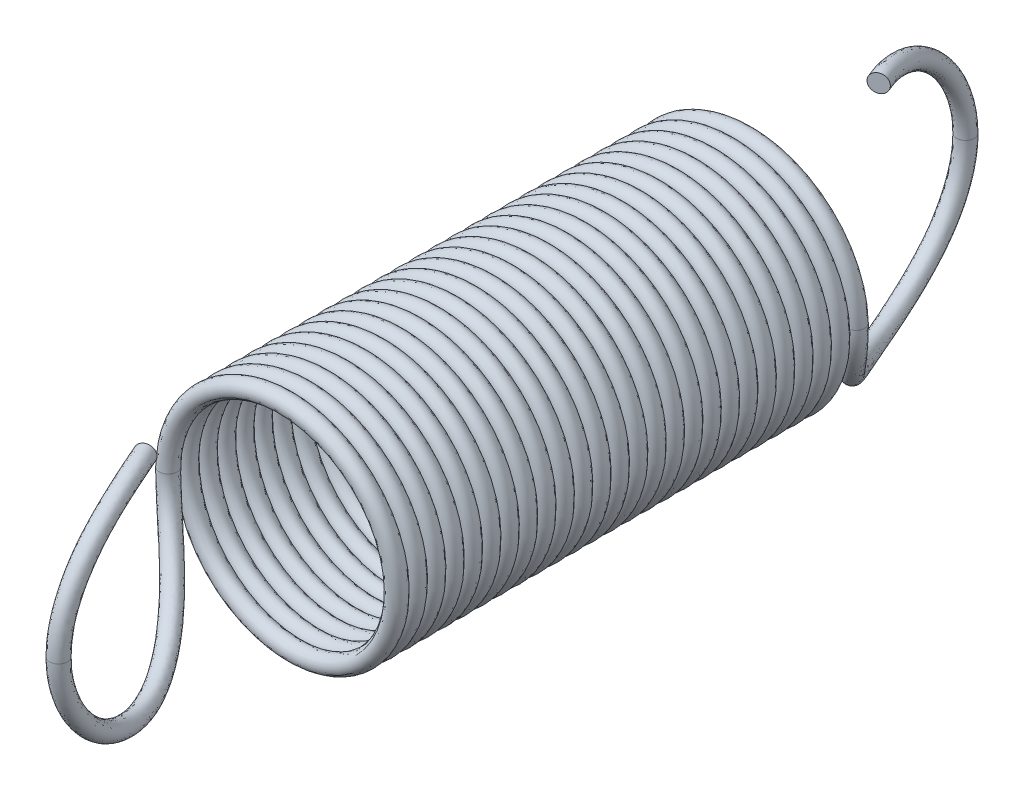
SolidWorks part; units mm, degrees
ref_plane "Front Plane" through (0, 0, 0) normal (0, 0, 1) x (1, 0, 0)
ref_plane "Top Plane" through (0, 0, 0) normal (0, 1, 0) x (1, 0, 0)
ref_plane "Right Plane" through (0, 0, 0) normal (1, 0, 0) x (0, 0, -1)
sketch "Sketch1" plane through (0, 0, 0) normal (1, 0, 0) x (0, 0, -1)
  line L0 (-7.5, 0) -> (7.5, 0) construction
  line L1 (7.5, 0) -> (40.99, 0) construction
  line L2 (-7.5, 2) -> (-7.5, -2) construction
  point P4 (0, 0)
  point P6 (-7.2, 0)
  point P9 (-7.5, 0)
  dimension "OD" = 4
  dimension "Wire Diameter" = 0.3
  dimension "Length" = 15
  dimension "Extended Length" = 48.49
sketch "Sketch2" plane through (0, 0, 0) normal (1, 0, 0) x (0, 0, -1)
  line L1 (-7.5, 0) -> (-7.8, 0) construction
  line L2 (-5.8, -1.7) -> (-5.8, -2) construction
  line L3 (0, 0) -> (0, 2) construction
  line L4 (-7.5, 0) -> (-7.2, 0) construction
  line L5 (-7.5, 0) -> (7.5, 0) construction
  line L6 (5.8, -1.7) -> (5.8, -2) construction
  line L7 (7.5, 0) -> (7.8, 0) construction
  line L8 (-5.8, -1.7) -> (5.8, -1.7) construction
  line L9 (-5.8, -2) -> (5.8, -2) construction
  line L10 (-3.8, 0) -> (-4.1, 0) construction
  line L11 (4.1, 0) -> (3.8, 0) construction
  line L12 (-7.5, 2) -> (-5.8, 2) construction
  circle A0 centre (-5.8, 0) radius 1.7 construction
  circle A2 centre (-5.8, 0) radius 2 construction
  circle A3 centre (5.8, 0) radius 2 construction
  circle A4 centre (5.8, 0) radius 1.7 construction
  point P7 (-2.6, 0)
  point P8 (-5.8, -1.85)
  point P10 (-7.65, 0)
  point P28 (7.65, 0)
  point P33 (-3.95, 0)
  point P34 (3.95, 0)
  point P35 (2.6, 0)
  dimension "OD" = 4
  dimension "D1" = 7.9
  dimension "D2" = 1.2
  dimension "D3" = 1.2
ref_plane "Plane1" through (0, 0, 3.95) normal (0, 0, 1) x (1, 0, 0)
sketch "Sketch3" plane through (0, 0, 3.95) normal (0, 0, 1) x (1, 0, 0)
  circle A0 centre (0, 0) radius 1.85
curve "Helix/Spiral1" pitch 0.3098 height 7.9 turns 25.5 parameters "Height"=7.9, "Pitch"=0.3098
sketch "Sketch4" plane through (0, 0, 0) normal (0, 1, 0) x (1, 0, 0)
  circle A0 centre (-1.85, -3.95) radius 0.15
  spline S0 degree 3 poles (-1.85, -3.95) (-1.85, -3.9436) (-1.7537, -3.9306) (-1.3422, -3.9113) (-0.7264, -3.8919) (0, -3.8725) (0.7264, -3.8532) (1.3422, -3.8338) (1.7537, -3.8145) (1.8982, -3.7951) (1.7537, -3.7757) (1.3422, -3.7564) (0.7264, -3.737) (0, -3.7176) (-0.7264, -3.6983) (-1.3422, -3.6789) (-1.7537, -3.6596) (-1.8982, -3.6402) (-1.7537, -3.6208) (-1.3422, -3.6015) (-0.7264, -3.5821) (0, -3.5627) (0.7264, -3.5434) (1.3422, -3.524) (1.7537, -3.5047) (1.8982, -3.4853) (1.7537, -3.4659) (1.3422, -3.4466) (0.7264, -3.4272) (0, -3.4078) (-0.7264, -3.3885) (-1.3422, -3.3691) (-1.7537, -3.3498) (-1.8982, -3.3304) (-1.7537, -3.311) (-1.3422, -3.2917) (-0.7264, -3.2723) (0, -3.2529) (0.7264, -3.2336) (1.3422, -3.2142) (1.7537, -3.1949) (1.8982, -3.1755) (1.7537, -3.1561) (1.3422, -3.1368) (0.7264, -3.1174) (0, -3.098) (-0.7264, -3.0787) (-1.3422, -3.0593) (-1.7537, -3.04) (-1.8982, -3.0206) (-1.7537, -3.0012) (-1.3422, -2.9819) (-0.7264, -2.9625) (0, -2.9431) (0.7264, -2.9238) (1.3422, -2.9044) (1.7537, -2.885) (1.8982, -2.8657) (1.7537, -2.8463) (1.3422, -2.827) (0.7264, -2.8076) (0, -2.7882) (-0.7264, -2.7689) (-1.3422, -2.7495) (-1.7537, -2.7301) (-1.8982, -2.7108) (-1.7537, -2.6914) (-1.3422, -2.6721) (-0.7264, -2.6527) (0, -2.6333) (0.7264, -2.614) (1.3422, -2.5946) (1.7537, -2.5752) (1.8982, -2.5559) (1.7537, -2.5365) (1.3422, -2.5172) (0.7264, -2.4978) (0, -2.4784) (-0.7264, -2.4591) (-1.3422, -2.4397) (-1.7537, -2.4203) (-1.8982, -2.401) (-1.7537, -2.3816) (-1.3422, -2.3623) (-0.7264, -2.3429) (0, -2.3235) (0.7264, -2.3042) (1.3422, -2.2848) (1.7537, -2.2654) (1.8982, -2.2461) (1.7537, -2.2267) (1.3422, -2.2074) (0.7264, -2.188) (0, -2.1686) (-0.7264, -2.1493) (-1.3422, -2.1299) (-1.7537, -2.1105) (-1.8982, -2.0912) (-1.7537, -2.0718) (-1.3422, -2.0525) (-0.7264, -2.0331) (0, -2.0137) (0.7264, -1.9944) (1.3422, -1.975) (1.7537, -1.9556) (1.8982, -1.9363) (1.7537, -1.9169) (1.3422, -1.8975) (0.7264, -1.8782) (0, -1.8588) (-0.7264, -1.8395) (-1.3422, -1.8201) (-1.7537, -1.8007) (-1.8982, -1.7814) (-1.7537, -1.762) (-1.3422, -1.7426) (-0.7264, -1.7233) (0, -1.7039) (0.7264, -1.6846) (1.3422, -1.6652) (1.7537, -1.6458) (1.8982, -1.6265) (1.7537, -1.6071) (1.3422, -1.5877) (0.7264, -1.5684) (0, -1.549) (-0.7264, -1.5297) (-1.3422, -1.5103) (-1.7537, -1.4909) (-1.8982, -1.4716) (-1.7537, -1.4522) (-1.3422, -1.4328) (-0.7264, -1.4135) (0, -1.3941) (0.7264, -1.3748) (1.3422, -1.3554) (1.7537, -1.336) (1.8982, -1.3167) (1.7537, -1.2973) (1.3422, -1.2779) (0.7264, -1.2586) (0, -1.2392) (-0.7264, -1.2199) (-1.3422, -1.2005) (-1.7537, -1.1811) (-1.8982, -1.1618) (-1.7537, -1.1424) (-1.3422, -1.123) (-0.7264, -1.1037) (0, -1.0843) (0.7264, -1.065) (1.3422, -1.0456) (1.7537, -1.0262) (1.8982, -1.0069) (1.7537, -0.9875) (1.3422, -0.9681) (0.7264, -0.9488) (0, -0.9294) (-0.7264, -0.91) (-1.3422, -0.8907) (-1.7537, -0.8713) (-1.8982, -0.852) (-1.7537, -0.8326) (-1.3422, -0.8132) (-0.7264, -0.7939) (0, -0.7745) (0.7264, -0.7551) (1.3422, -0.7358) (1.7537, -0.7164) (1.8982, -0.6971) (1.7537, -0.6777) (1.3422, -0.6583) (0.7264, -0.639) (0, -0.6196) (-0.7264, -0.6002) (-1.3422, -0.5809) (-1.7537, -0.5615) (-1.8982, -0.5422) (-1.7537, -0.5228) (-1.3422, -0.5034) (-0.7264, -0.4841) (0, -0.4647) (0.7264, -0.4453) (1.3422, -0.426) (1.7537, -0.4066) (1.8982, -0.3873) (1.7537, -0.3679) (1.3422, -0.3485) (0.7264, -0.3292) (0, -0.3098) (-0.7264, -0.2904) (-1.3422, -0.2711) (-1.7537, -0.2517) (-1.8982, -0.2324) (-1.7537, -0.213) (-1.3422, -0.1936) (-0.7264, -0.1743) (0, -0.1549) (0.7264, -0.1355) (1.3422, -0.1162) (1.7537, -0.0968) (1.8982, -0.0775) (1.7537, -0.0581) (1.3422, -0.0387) (0.7264, -0.0194) (0, 0) (-0.7264, 0.0194) (-1.3422, 0.0387) (-1.7537, 0.0581) (-1.8982, 0.0775) (-1.7537, 0.0968) (-1.3422, 0.1162) (-0.7264, 0.1355) (0, 0.1549) (0.7264, 0.1743) (1.3422, 0.1936) (1.7537, 0.213) (1.8982, 0.2324) (1.7537, 0.2517) (1.3422, 0.2711) (0.7264, 0.2904) (0, 0.3098) (-0.7264, 0.3292) (-1.3422, 0.3485) (-1.7537, 0.3679) (-1.8982, 0.3873) (-1.7537, 0.4066) (-1.3422, 0.426) (-0.7264, 0.4453) (0, 0.4647) (0.7264, 0.4841) (1.3422, 0.5034) (1.7537, 0.5228) (1.8982, 0.5422) (1.7537, 0.5615) (1.3422, 0.5809) (0.7264, 0.6002) (0, 0.6196) (-0.7264, 0.639) (-1.3422, 0.6583) (-1.7537, 0.6777) (-1.8982, 0.6971) (-1.7537, 0.7164) (-1.3422, 0.7358) (-0.7264, 0.7551) (0, 0.7745) (0.7264, 0.7939) (1.3422, 0.8132) (1.7537, 0.8326) (1.8982, 0.852) (1.7537, 0.8713) (1.3422, 0.8907) (0.7264, 0.91) (0, 0.9294) (-0.7264, 0.9488) (-1.3422, 0.9681) (-1.7537, 0.9875) (-1.8982, 1.0069) (-1.7537, 1.0262) (-1.3422, 1.0456) (-0.7264, 1.065) (0, 1.0843) (0.7264, 1.1037) (1.3422, 1.123) (1.7537, 1.1424) (1.8982, 1.1618) (1.7537, 1.1811) (1.3422, 1.2005) (0.7264, 1.2199) (0, 1.2392) (-0.7264, 1.2586) (-1.3422, 1.2779) (-1.7537, 1.2973) (-1.8982, 1.3167) (-1.7537, 1.336) (-1.3422, 1.3554) (-0.7264, 1.3748) (0, 1.3941) (0.7264, 1.4135) (1.3422, 1.4328) (1.7537, 1.4522) (1.8982, 1.4716) (1.7537, 1.4909) (1.3422, 1.5103) (0.7264, 1.5297) (0, 1.549) (-0.7264, 1.5684) (-1.3422, 1.5877) (-1.7537, 1.6071) (-1.8982, 1.6265) (-1.7537, 1.6458) (-1.3422, 1.6652) (-0.7264, 1.6846) (0, 1.7039) (0.7264, 1.7233) (1.3422, 1.7426) (1.7537, 1.762) (1.8982, 1.7814) (1.7537, 1.8007) (1.3422, 1.8201) (0.7264, 1.8395) (0, 1.8588) (-0.7264, 1.8782) (-1.3422, 1.8975) (-1.7537, 1.9169) (-1.8982, 1.9363) (-1.7537, 1.9556) (-1.3422, 1.975) (-0.7264, 1.9944) (0, 2.0137) (0.7264, 2.0331) (1.3422, 2.0525) (1.7537, 2.0718) (1.8982, 2.0912) (1.7537, 2.1105) (1.3422, 2.1299) (0.7264, 2.1493) (0, 2.1686) (-0.7264, 2.188) (-1.3422, 2.2074) (-1.7537, 2.2267) (-1.8982, 2.2461) (-1.7537, 2.2654) (-1.3422, 2.2848) (-0.7264, 2.3042) (0, 2.3235) (0.7264, 2.3429) (1.3422, 2.3623) (1.7537, 2.3816) (1.8982, 2.401) (1.7537, 2.4203) (1.3422, 2.4397) (0.7264, 2.4591) (0, 2.4784) (-0.7264, 2.4978) (-1.3422, 2.5172) (-1.7537, 2.5365) (-1.8982, 2.5559) (-1.7537, 2.5752) (-1.3422, 2.5946) (-0.7264, 2.614) (0, 2.6333) (0.7264, 2.6527) (1.3422, 2.6721) (1.7537, 2.6914) (1.8982, 2.7108) (1.7537, 2.7301) (1.3422, 2.7495) (0.7264, 2.7689) (0, 2.7882) (-0.7264, 2.8076) (-1.3422, 2.827) (-1.7537, 2.8463) (-1.8982, 2.8657) (-1.7537, 2.885) (-1.3422, 2.9044) (-0.7264, 2.9238) (0, 2.9431) (0.7264, 2.9625) (1.3422, 2.9819) (1.7537, 3.0012) (1.8982, 3.0206) (1.7537, 3.04) (1.3422, 3.0593) (0.7264, 3.0787) (0, 3.098) (-0.7264, 3.1174) (-1.3422, 3.1368) (-1.7537, 3.1561) (-1.8982, 3.1755) (-1.7537, 3.1949) (-1.3422, 3.2142) (-0.7264, 3.2336) (0, 3.2529) (0.7264, 3.2723) (1.3422, 3.2917) (1.7537, 3.311) (1.8982, 3.3304) (1.7537, 3.3498) (1.3422, 3.3691) (0.7264, 3.3885) (0, 3.4078) (-0.7264, 3.4272) (-1.3422, 3.4466) (-1.7537, 3.4659) (-1.8982, 3.4853) (-1.7537, 3.5047) (-1.3422, 3.524) (-0.7264, 3.5434) (0, 3.5627) (0.7264, 3.5821) (1.3422, 3.6015) (1.7537, 3.6208) (1.8982, 3.6402) (1.7537, 3.6596) (1.3422, 3.6789) (0.7264, 3.6983) (0, 3.7176) (-0.7264, 3.737) (-1.3422, 3.7564) (-1.7537, 3.7757) (-1.8982, 3.7951) (-1.7537, 3.8145) (-1.3422, 3.8338) (-0.7264, 3.8532) (0, 3.8725) (0.7264, 3.8919) (1.3422, 3.9113) (1.7537, 3.9306) (1.85, 3.9436) (1.85, 3.95) knots 0 0 0 0 0.002451 0.004902 0.007353 0.009804 0.012255 0.014706 0.017157 0.019608 0.022059 0.02451 0.026961 0.029412 0.031863 0.034314 0.036765 0.039216 0.041667 0.044118 0.046569 0.04902 0.051471 0.053922 0.056373 0.058824 0.061275 0.063725 0.066176 0.068627 0.071078 0.073529 0.07598 0.078431 0.080882 0.083333 0.085784 0.088235 0.090686 0.093137 0.095588 0.098039 0.10049 0.102941 0.105392 0.107843 0.110294 0.112745 0.115196 0.117647 0.120098 0.122549 0.125 0.127451 0.129902 0.132353 0.134804 0.137255 0.139706 0.142157 0.144608 0.147059 0.14951 0.151961 0.154412 0.156863 0.159314 0.161765 0.164216 0.166667 0.169118 0.171569 0.17402 0.176471 0.178922 0.181373 0.183824 0.186275 0.188725 0.191176 0.193627 0.196078 0.198529 0.20098 0.203431 0.205882 0.208333 0.210784 0.213235 0.215686 0.218137 0.220588 0.223039 0.22549 0.227941 0.230392 0.232843 0.235294 0.237745 0.240196 0.242647 0.245098 0.247549 0.25 0.252451 0.254902 0.257353 0.259804 0.262255 0.264706 0.267157 0.269608 0.272059 0.27451 0.276961 0.279412 0.281863 0.284314 0.286765 0.289216 0.291667 0.294118 0.296569 0.29902 0.301471 0.303922 0.306373 0.308824 0.311275 0.313725 0.316176 0.318627 0.321078 0.323529 0.32598 0.328431 0.330882 0.333333 0.335784 0.338235 0.340686 0.343137 0.345588 0.348039 0.35049 0.352941 0.355392 0.357843 0.360294 0.362745 0.365196 0.367647 0.370098 0.372549 0.375 0.377451 0.379902 0.382353 0.384804 0.387255 0.389706 0.392157 0.394608 0.397059 0.39951 0.401961 0.404412 0.406863 0.409314 0.411765 0.414216 0.416667 0.419118 0.421569 0.42402 0.426471 0.428922 0.431373 0.433824 0.436275 0.438725 0.441176 0.443627 0.446078 0.448529 0.45098 0.453431 0.455882 0.458333 0.460784 0.463235 0.465686 0.468137 0.470588 0.473039 0.47549 0.477941 0.480392 0.482843 0.485294 0.487745 0.490196 0.492647 0.495098 0.497549 0.5 0.502451 0.504902 0.507353 0.509804 0.512255 0.514706 0.517157 0.519608 0.522059 0.52451 0.526961 0.529412 0.531863 0.534314 0.536765 0.539216 0.541667 0.544118 0.546569 0.54902 0.551471 0.553922 0.556373 0.558824 0.561275 0.563725 0.566176 0.568627 0.571078 0.573529 0.57598 0.578431 0.580882 0.583333 0.585784 0.588235 0.590686 0.593137 0.595588 0.598039 0.60049 0.602941 0.605392 0.607843 0.610294 0.612745 0.615196 0.617647 0.620098 0.622549 0.625 0.627451 0.629902 0.632353 0.634804 0.637255 0.639706 0.642157 0.644608 0.647059 0.64951 0.651961 0.654412 0.656863 0.659314 0.661765 0.664216 0.666667 0.669118 0.671569 0.67402 0.676471 0.678922 0.681373 0.683824 0.686275 0.688725 0.691176 0.693627 0.696078 0.698529 0.70098 0.703431 0.705882 0.708333 0.710784 0.713235 0.715686 0.718137 0.720588 0.723039 0.72549 0.727941 0.730392 0.732843 0.735294 0.737745 0.740196 0.742647 0.745098 0.747549 0.75 0.752451 0.754902 0.757353 0.759804 0.762255 0.764706 0.767157 0.769608 0.772059 0.77451 0.776961 0.779412 0.781863 0.784314 0.786765 0.789216 0.791667 0.794118 0.796569 0.79902 0.801471 0.803922 0.806373 0.808824 0.811275 0.813725 0.816176 0.818627 0.821078 0.823529 0.82598 0.828431 0.830882 0.833333 0.835784 0.838235 0.840686 0.843137 0.845588 0.848039 0.85049 0.852941 0.855392 0.857843 0.860294 0.862745 0.865196 0.867647 0.870098 0.872549 0.875 0.877451 0.879902 0.882353 0.884804 0.887255 0.889706 0.892157 0.894608 0.897059 0.89951 0.901961 0.904412 0.906863 0.909314 0.911765 0.914216 0.916667 0.919118 0.921569 0.92402 0.926471 0.928922 0.931373 0.933824 0.936275 0.938725 0.941176 0.943627 0.946078 0.948529 0.95098 0.953431 0.955882 0.958333 0.960784 0.963235 0.965686 0.968137 0.970588 0.973039 0.97549 0.977941 0.980392 0.982843 0.985294 0.987745 0.990196 0.992647 0.995098 0.997549 1 1 1 1 construction
  dimension "D1" = 0.3
sweep "Spring Body Sweep" add profiles "Sketch4" path "Helix/Spiral1"
sketch "Sketch5" plane through (0, 0, 0) normal (1, 0, 0) x (0, 0, -1)
  line L0 (-4.1, 0) -> (-3.8, 0) construction
  line L1 (-4.1, 0) -> (-3.8, 0) construction
  line L2 (-7.5, 0) -> (7.5, 0) construction
  arc A1 (-3.95, 0) -> (-5.8, 1.85) centre (-5.8, 0) cw
sketch "Sketch6" plane through (0, 0, 0) normal (0, 1, 0) x (1, 0, 0)
  line L2 (-1.85, -3.8) -> (-1.85, -4.1) construction
  line L3 (-1.85, -3.95) -> (1.85, -3.95) construction
  line L4 (0, -7.5) -> (0, -7.8) construction
  line L5 (0, -7.65) -> (0, -3.95) construction
  arc A2 (-1.85, -3.95) -> (0, -7.65) centre (-4.625, -7.65) cw
sketch "Sketch7" plane through (0, 0, 0) normal (0, -1, 0) x (1, 0, 0)
  circle A1 centre (-1.85, 3.95) radius 0.15
  circle A3 centre (-1.85, 3.95) radius 0.15
  dimension "D1" = 0
ref_axis "Axis1" through (0, 2.5403, 0) along (0, -1, 0)
curve "Curve1"
sweep "Spring Hook Sweep" add profiles "Sketch7" path "Curve1"
pattern_circular "Spring Hook CirPattern" count 2 over 360 about axis through (0, 2.5403, 0) along (0, -1, 0) of "Spring Hook Sweep"
equation "\"D1@Sketch4\" = \"Wire Diameter@Sketch1\""
equation "\"Height@Helix/Spiral1\"=\"D1@Sketch2\""
equation "\"D2@Sketch2\" = 4 * \"Wire Diameter@Sketch1\""
equation "\"D3@Sketch2\"=\"D2@Sketch2\""
